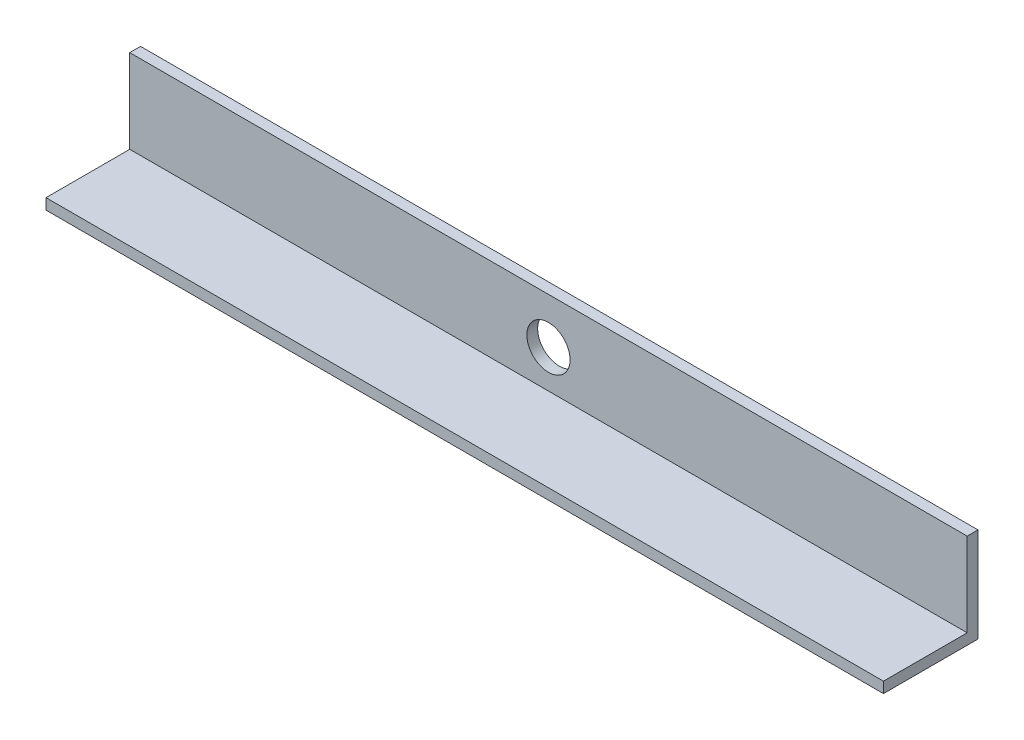
SolidWorks part; units mm, degrees
ref_plane "Спереди" through (0, 0, 0) normal (0, 0, 1) x (1, 0, 0)
ref_plane "Сверху" through (0, 0, 0) normal (0, 1, 0) x (1, 0, 0)
ref_plane "Справа" through (0, 0, 0) normal (1, 0, 0) x (0, 0, -1)
sketch "Эскиз1" plane through (0, 0, 0) normal (1, 0, 0) x (0, 0, -1)
  line L0 (0, 35) -> (0, 0)
  line L1 (0, 0) -> (-35, 0)
extrude "Вытянуть-Тонкостенный1" add sketch "Эскиз1" along normal blind 310 thin
sketch "Эскиз2" plane through (0, 0, 0) normal (0, 0, -1) x (-1, 0, 0)
  circle A0 centre (-155, 18) radius 8
extrude "Вырез-Вытянуть1" cut sketch "Эскиз2" against normal blind 10
